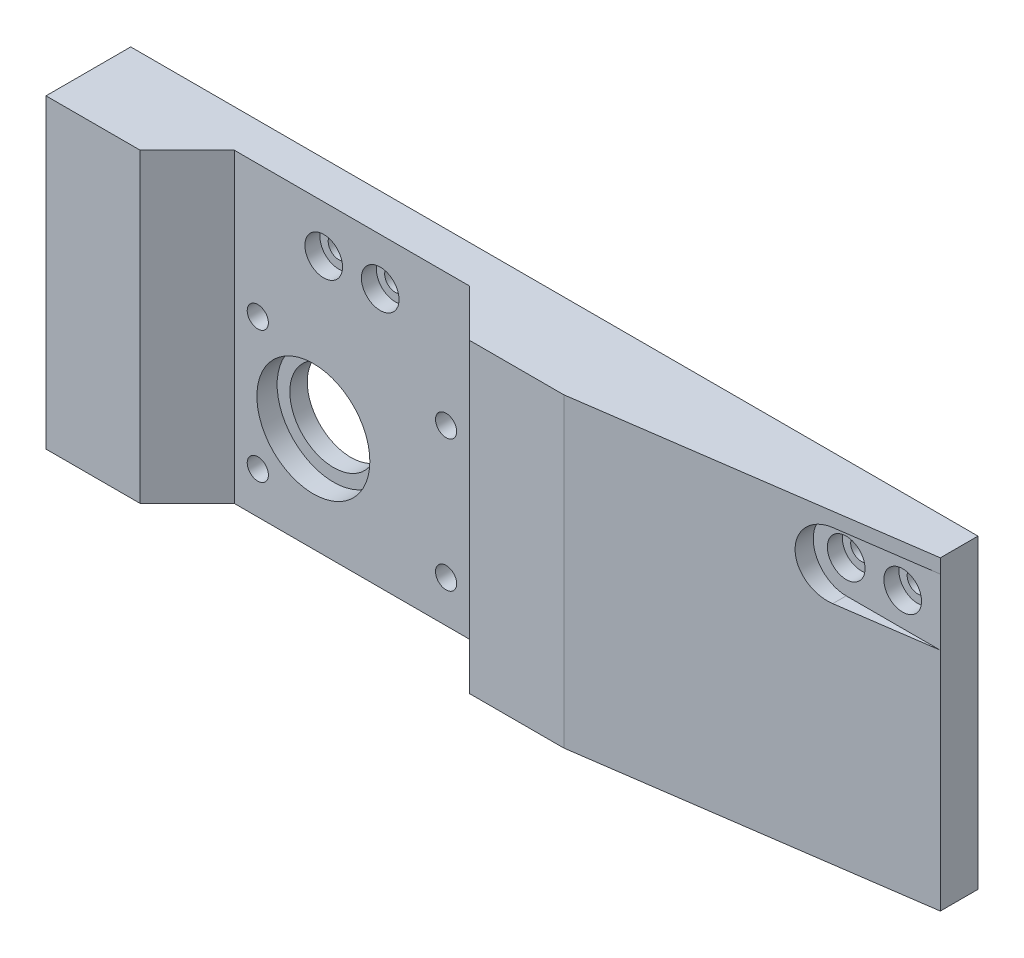
SolidWorks part; units mm, degrees
material "ABS"
ref_plane "Front Plane" through (0, 0, 0) normal (0, 0, 1) x (1, 0, 0)
ref_plane "Top Plane" through (0, 0, 0) normal (0, 1, 0) x (1, 0, 0)
ref_plane "Right Plane" through (0, 0, 0) normal (1, 0, 0) x (0, 0, -1)
sketch "Sketch2" plane through (0, 0, 0) normal (0, 1, 0) x (1, 0, 0)
  line L0 (180, 0) -> (0, 0)
  line L1 (0, 0) -> (0, -18)
  line L2 (0, -18) -> (20, -18)
  line L3 (20, -18) -> (30, -8)
  line L5 (180, -8) -> (180, 0)
  line L6 (30, -8) -> (80, -8)
  line L7 (80, -8) -> (90, -18)
  line L8 (90, -18) -> (110, -18)
  line L9 (110, -18) -> (180, -8)
  dimension "D1" = 180
  dimension "D2" = 8
  dimension "D3" = 20
  dimension "D4" = 20
  dimension "D5" = 18
  dimension "D6" = 50
  dimension "D7" = 45
  dimension "D8" = 45
extrude "Boss-Extrude1" add sketch "Sketch2" along normal blind 65
hole_wizard "Ø4.0mm Dowel Hole1" positions "Sketch3" profile "Sketch4" hole size "Ø4.0" standard "DIN"
sketch "Sketch3" plane through (0, 0, 0) normal (0, -1, 0) x (-1, 0, 0)
  line L0 (0, -18) -> (-20, -18) construction
  line L3 (0, 0) -> (0, -18) construction
  line L5 (-180, 0) -> (0, 0) construction
  point P0 (-5, -13)
  point P2 (-15, -13)
  point P4 (-95, -13)
  point P6 (-105, -13)
  point P16 (-10, -18)
  point P20 (-22.5, -5)
  point P22 (-87.5, -5)
  dimension "D1" = 5
  dimension "D2" = 5
  dimension "D3" = 10
  dimension "D4" = 10
  dimension "D5" = 5
  dimension "D6" = 7.5
  dimension "D7" = 5
  dimension "D8" = 7.5
sketch "Sketch4" plane through (5, 0, 13) normal (1, 0, 0) x (0, 0, -1)
  line L0 (0, 0) -> (0, 8.3017)
  line L1 (0, 8.3017) -> (2, 7.1)
  line L2 (2, 7.1) -> (2, 0)
  line L5 (2, 0) -> (0, 0)
  line L10 (0, 8.3017) -> (-2, 7.1) construction
  line L11 (0, -6.35) -> (0, 107.95) construction
  dimension "Hole Dia." = 4
  dimension "Hole Depth" = 7.1
  dimension "Drill Angle" = 118
sketch "Sketch5" plane through (0, 0, 0) normal (0, 0, 1) x (1, 0, 0)
  line L0 (180, 55) -> (160, 55) construction
  line L1 (180, 65) -> (180, 0) construction
  line L2 (180, 48) -> (160, 48)
  line L3 (180, 62) -> (160, 62)
  line L4 (110, 65) -> (180, 65) construction
  arc A0 (180, 48) -> (180, 62) centre (180, 55) ccw
  arc A1 (160, 62) -> (160, 48) centre (160, 55) ccw
  point P4 (170, 55)
  dimension "D1" = 14
  dimension "D2" = 20
  dimension "D3" = 10
extrude "Cut-Extrude1" cut sketch "Sketch5" along normal blind 8 from offset 8
hole_wizard "CBORE for M4 Hex Socket Head Cap Screw1" positions "Sketch6" profile "Sketch7" counterbore size "M4" standard "DIN" end condition up to next
sketch "Sketch6" plane through (0, 0, 8) normal (0, 0, 1) x (1, 0, 0)
  line L0 (30, 65) -> (80, 65) construction
  point P0 (160, 55)
  point P3 (172, 55)
  point P7 (49, 55)
  point P9 (61, 55)
  point P14 (55, 65)
  dimension "D1" = 12
  dimension "D2" = 6
  dimension "D3" = 6
sketch "Sketch7" plane through (160, 55, 8) normal (1, 0, 0) x (0, -1, 0)
  line L0 (0, 0) -> (0, 8)
  line L1 (0, 8) -> (2.25, 8)
  line L3 (2.25, 8) -> (2.25, 3.2)
  line L4 (2.25, 3.2) -> (4, 3.2)
  line L5 (4, 3.2) -> (4, 0)
  line L7 (4, 0) -> (0, 0)
  line L11 (0, -6.35) -> (0, 107.95) construction
  dimension "Thru Hole Dia." = 4.5
  dimension "Thru Hole Depth" = 8
  dimension "C'Bore Dia." = 8
  dimension "C'Bore Depth" = 3.2
sketch "Sketch8" plane through (0, 0, 8) normal (0, 0, 1) x (1, 0, 0)
  line L0 (30, 0) -> (80, 0) construction
  line L2 (30, 65) -> (80, 65) construction
  circle A0 centre (46.8, 22.15) radius 12
  point P8 (55, 65)
  dimension "D2" = 24
  dimension "D1" = 22.15
  dimension "D3" = 8.2
extrude "Cut-Extrude2" cut sketch "Sketch8" against normal blind 4.3
sketch "Sketch9" plane through (0, 0, 3.7) normal (0, 0, 1) x (1, 0, 0)
  circle A0 centre (46.8, 22.15) radius 9.3
  dimension "D1" = 18.6
extrude "Cut-Extrude3" cut sketch "Sketch9" against normal up to next
hole_wizard "M4 Clearance Hole1" positions "Sketch10" profile "Sketch11" hole size "M4" standard "DIN" end condition up to next
sketch "Sketch10" plane through (0, 0, 8) normal (0, 0, 1) x (1, 0, 0)
  line L0 (30, 0) -> (80, 0) construction
  point P0 (35, 36.8539)
  point P2 (75, 36.8539)
  point P4 (75, 8.8539)
  point P6 (35, 8.8539)
  point P11 (55, 0)
  dimension "D1" = 20
  dimension "D2" = 40
  dimension "D3" = 28
sketch "Sketch11" plane through (35, 36.8539, 8) normal (1, 0, 0) x (0, -1, 0)
  line L0 (0, 0) -> (0, 8)
  line L1 (0, 8) -> (2.25, 8)
  line L2 (2.25, 8) -> (2.25, 0)
  line L5 (2.25, 0) -> (0, 0)
  line L11 (0, -6.35) -> (0, 107.95) construction
  dimension "Thru Hole Dia." = 4.5
  dimension "Thru Hole Depth" = 8
